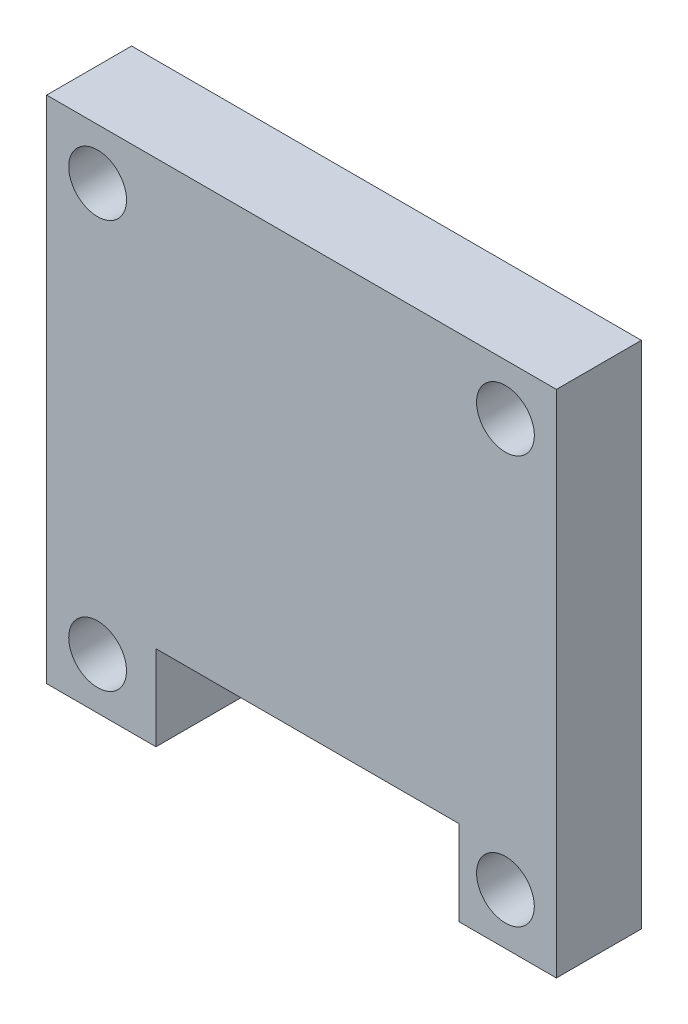
SolidWorks part; units mm, degrees
ref_plane "Front Plane" through (0, 0, 0) normal (0, 0, 1) x (1, 0, 0)
ref_plane "Top Plane" through (0, 0, 0) normal (0, 1, 0) x (1, 0, 0)
ref_plane "Right Plane" through (0, 0, 0) normal (1, 0, 0) x (0, 0, -1)
sketch "Sketch1" plane through (0, 0, 0) normal (0, 0, 1) x (1, 0, 0)
  line L0 (15, 30) -> (15, 0) construction
  line L1 (0, 0) -> (30, 0)
  line L2 (0, 0) -> (0, 30)
  line L3 (0, 30) -> (30, 30)
  line L4 (30, 0) -> (30, 30)
  line L5 (0, 15) -> (30, 15) construction
  circle A0 centre (3, 27) radius 1.7
  circle A1 centre (27, 27) radius 1.7
  circle A2 centre (27, 3) radius 1.7
  circle A3 centre (3, 3) radius 1.7
  dimension "D5" = 3.4
  dimension "D1" = 30
  dimension "D2" = 30
  dimension "D3" = 3
  dimension "D4" = 3
extrude "Boss-Extrude1" add sketch "Sketch1" along normal blind 5 contours L2 L3 L4 L1 | A0 | A3 | A2 | A1
sketch "Sketch3" plane through (0, 0, 5) normal (0, 0, 1) x (1, 0, 0)
  line L0 (0, 0) -> (30, 0) construction
  line L1 (6.4347, 0) -> (24.2653, 0)
  line L2 (6.4347, 0) -> (6.4347, 5)
  line L3 (6.4347, 5) -> (24.2653, 5)
  line L4 (24.2653, 0) -> (24.2653, 5)
  dimension "D1" = 5
extrude "Cut-Extrude1" cut sketch "Sketch3" against normal blind 5
